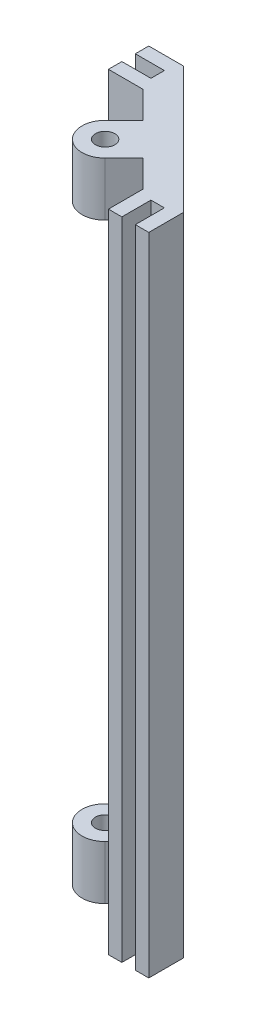
SolidWorks part; units mm, degrees
ref_plane "Front Plane" through (0, 0, 0) normal (0, 0, 1) x (1, 0, 0)
ref_plane "Top Plane" through (0, 0, 0) normal (0, 1, 0) x (1, 0, 0)
ref_plane "Right Plane" through (0, 0, 0) normal (1, 0, 0) x (0, 0, -1)
sketch "Sketch1" plane through (0, 0, 0) normal (0, 1, 0) x (1, 0, 0)
  line L0 (0, 0) -> (31.75, 0) construction
  line L1 (38.1, 0) -> (38.1, 25.4) construction
  line L2 (25.4, 38.1) -> (0, 38.1) construction
  line L3 (0, 38.1) -> (0, 34.925) construction
  line L4 (38.1, 0) -> (38.1, 8.2099)
  line L5 (38.1, 8.2099) -> (8.2099, 38.1)
  line L6 (8.2099, 38.1) -> (0, 38.1)
  line L7 (0, 38.1) -> (0, 34.925)
  line L8 (0, 28.575) -> (8.2099, 28.575)
  line L9 (8.2099, 28.575) -> (14.5309, 22.2539)
  line L10 (28.575, 8.2099) -> (28.575, 0)
  line L11 (28.575, 0) -> (31.75, 0)
  line L12 (34.3803, 34.3803) -> (23.1549, 23.1549) construction
  line L13 (0, 31.75) -> (0, 0) construction
  line L15 (31.75, 0) -> (31.75, 6.858)
  line L16 (31.75, 6.858) -> (34.925, 6.858)
  line L17 (34.925, 0) -> (34.925, 6.858)
  line L22 (0, 31.75) -> (6.858, 31.75)
  line L24 (0, 34.925) -> (6.858, 34.925)
  line L25 (6.858, 31.75) -> (6.858, 34.925)
  line L26 (0, 31.75) -> (0, 28.575)
  line L27 (34.925, 0) -> (38.1, 0) construction
  line L28 (34.925, 0) -> (38.1, 0)
  line L29 (14.5309, 22.2539) -> (10.0408, 17.7638)
  line L31 (17.7638, 10.0408) -> (22.2539, 14.5309)
  line L32 (22.2539, 14.5309) -> (28.575, 8.2099)
  arc A0 (10.0408, 17.7638) -> (17.7638, 10.0408) centre (13.9023, 13.9023) ccw
  circle A1 centre (13.9023, 13.9023) radius 2.286
  arc A2 (38.1, 25.4) -> (25.4, 38.1) centre (25.4, 25.4) ccw construction
  dimension "D4" = 4.572
  dimension "D9" = 3.175
  dimension "D12" = 6.7352
  dimension "D10" = 10.922
  dimension "D13" = 12.7
  dimension "D1" = 38.1
  dimension "D2" = 38.1
  dimension "D3" = 3.175
  dimension "D5" = 3.175
  dimension "D6" = 3.175
  dimension "D7" = 3.175
  dimension "D8" = 6.858
  dimension "D11" = 6.35
  dimension "D14" = 15.875
  dimension "D15" = 13.0852
  dimension "D16" = 28.9602
extrude "Boss-Extrude1" add sketch "Sketch1" along normal blind 152.4
sketch "Sketch2" plane through (18.3924, 0, -18.3924) normal (-0.7071, 0, 0.7071) x (0.7071, 0, 0.7071)
  line L0 (5.461, 152.4) -> (5.461, 0) construction
  line L1 (5.461, 12.7) -> (-5.461, 12.7)
  line L2 (5.461, 12.7) -> (5.461, 139.7)
  line L3 (5.461, 139.7) -> (-5.461, 139.7)
  line L4 (-5.461, 12.7) -> (-5.461, 139.7)
  line L5 (-5.461, 152.4) -> (-5.461, 0) construction
  line L6 (5.461, 152.4) -> (-5.461, 152.4) construction
  line L7 (-5.461, 0) -> (5.461, 0) construction
  dimension "D1" = 12.7
  dimension "D2" = 12.7
extrude "Cut-Extrude1" cut sketch "Sketch2" along normal up to vertex
sketch "Sketch3" plane through (18.3924, 0, -18.3924) normal (-0.7071, 0, 0.7071) x (0.7071, 0, 0.7071)
  line L1 (-5.461, 139.7) -> (5.461, 139.7) construction
  line L2 (-3.175, 139.7) -> (3.175, 139.7)
  line L3 (-3.175, 139.7) -> (-3.175, 12.7)
  line L4 (-3.175, 12.7) -> (3.175, 12.7)
  line L5 (3.175, 139.7) -> (3.175, 12.7)
  line L6 (-5.461, 12.7) -> (5.461, 12.7) construction
  point P0 (0, 12.7)
  dimension "D1" = 6.35
extrude "Boss-Extrude2" add sketch "Sketch3" along normal blind 1.27
